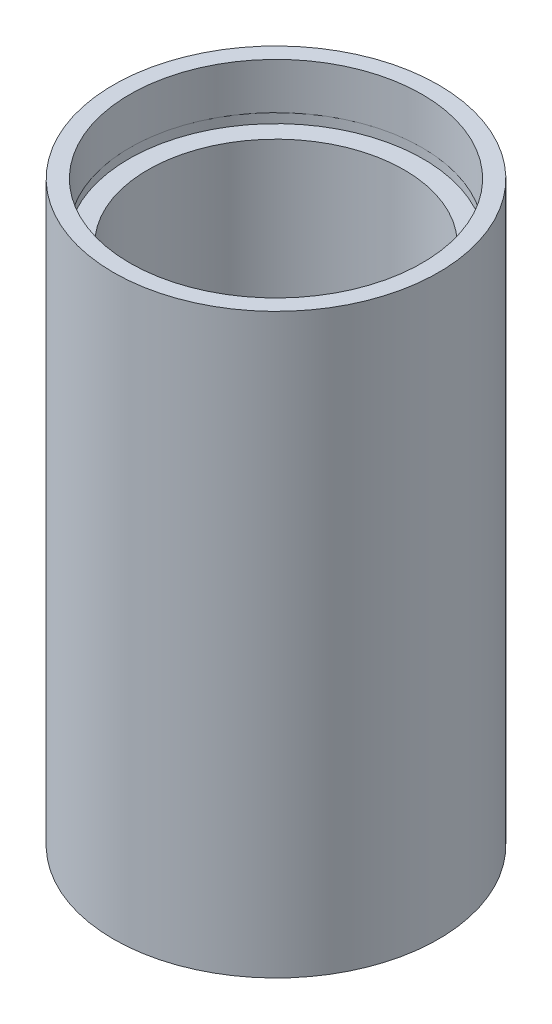
SolidWorks part; units mm, degrees
ref_plane "前视基准面" through (0, 0, 0) normal (0, 0, 1) x (1, 0, 0)
ref_plane "上视基准面" through (0, 0, 0) normal (0, 1, 0) x (1, 0, 0)
ref_plane "右视基准面" through (0, 0, 0) normal (1, 0, 0) x (0, 0, -1)
sketch "草图1" plane through (0, 0, 0) normal (0, 0, 1) x (1, 0, 0)
  line L0 (0, 161.3762) -> (0, 0) construction
  line L1 (141.7365, 0) -> (-131.7984, 0) construction
  line L2 (13.75, 0) -> (13.75, 4.5)
  line L3 (15.85, 0) -> (15.85, 56.3)
  line L4 (14.35, 4.5) -> (14.35, 5.5)
  line L5 (13.75, 4.5) -> (14.35, 4.5)
  line L6 (12.5, 5.5) -> (12.5, 50.8)
  line L7 (12.5, 5.5) -> (14.35, 5.5)
  line L8 (14.25, 56.3) -> (14.25, 51.8)
  line L9 (15.85, 56.3) -> (14.25, 56.3)
  line L10 (14.35, 51.8) -> (14.35, 50.8)
  line L11 (14.25, 51.8) -> (14.35, 51.8)
  line L12 (12.5, 50.8) -> (14.35, 50.8)
  line L13 (13.75, 0) -> (15.85, 0)
  dimension "D1" = 13.75
  dimension "D2" = 15.85
  dimension "D3" = 14.35
  dimension "D4" = 12.5
  dimension "D5" = 4.5
  dimension "D6" = 1
  dimension "D7" = 50.8
  dimension "D8" = 14.25
  dimension "D9" = 14.35
  dimension "D10" = 1
  dimension "D11" = 4.5
revolve "旋转1" add sketch "草图1" angle 360 about L0
cosmetic thread "装饰螺纹线1" parameters "D2"=28.5
cosmetic thread "装饰螺纹线2" parameters "D2"=26
cosmetic thread "装饰螺纹线3" parameters "D2"=28.51
